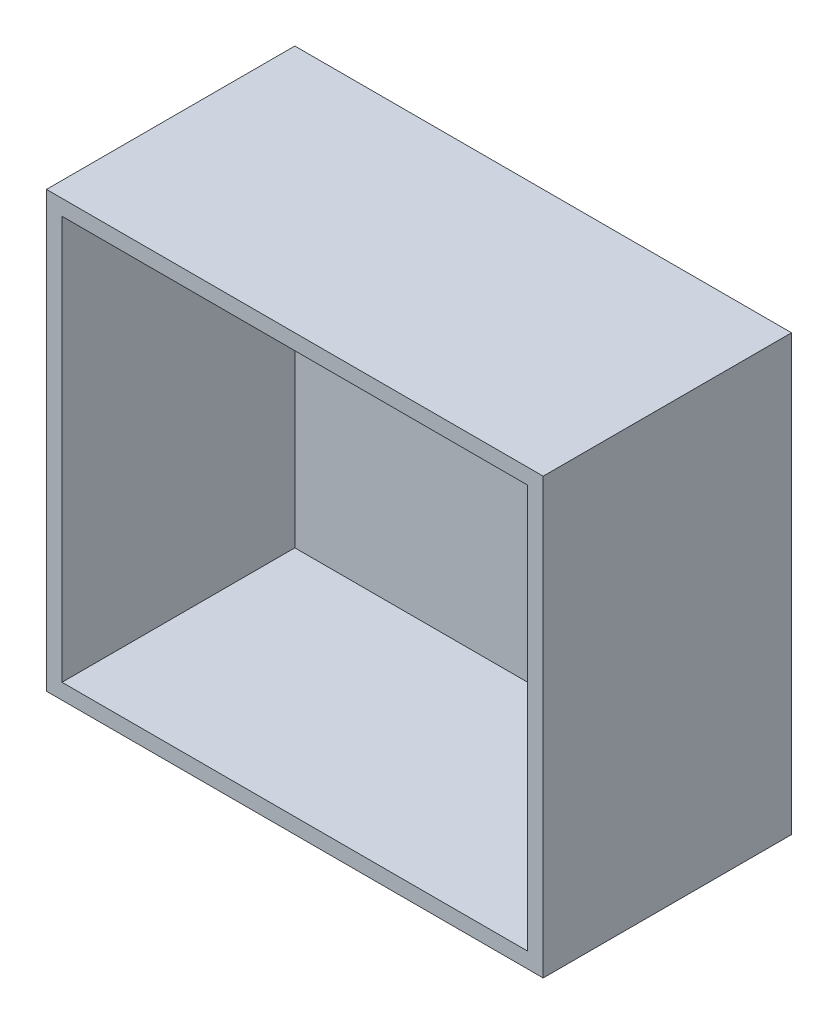
SolidWorks part; units mm, degrees
ref_plane "Front Plane" through (0, 0, 0) normal (0, 0, 1) x (1, 0, 0)
ref_plane "Top Plane" through (0, 0, 0) normal (0, 1, 0) x (1, 0, 0)
ref_plane "Right Plane" through (0, 0, 0) normal (1, 0, 0) x (0, 0, -1)
sketch "Sketch1" plane through (0, 0, 0) normal (0, 0, 1) x (1, 0, 0)
  line L1 (0, 0) -> (64, 0)
  line L2 (0, 0) -> (0, 56)
  line L3 (0, 56) -> (64, 56)
  line L4 (64, 0) -> (64, 56)
  dimension "D1" = 64
  dimension "D2" = 56
extrude "Boss-Extrude1" add sketch "Sketch1" along normal blind 32
sketch "Sketch3" plane through (0, 0, 32) normal (0, 0, 1) x (1, 0, 0)
  line L0 (64, 56) -> (0, 56) construction
  line L1 (2, 54) -> (62, 54)
  line L2 (2, 54) -> (2, 2)
  line L3 (2, 2) -> (62, 2)
  line L4 (62, 54) -> (62, 2)
  line L5 (0, 56) -> (0, 0) construction
  dimension "D1" = 60
  dimension "D2" = 52
  dimension "D3" = 2
  dimension "D4" = 2
extrude "Cut-Extrude1" cut sketch "Sketch3" against normal blind 30
